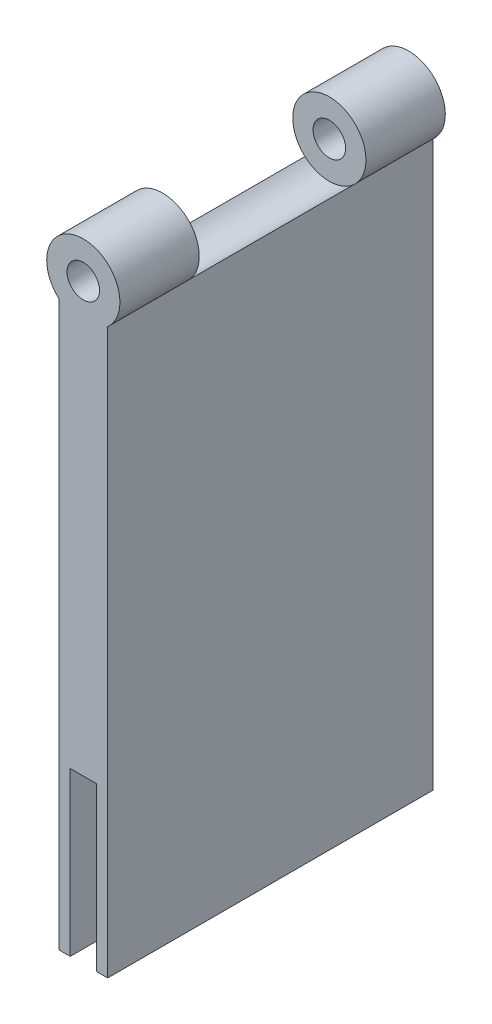
SolidWorks part; units mm, degrees
ref_plane "Front Plane" through (0, 0, 0) normal (0, 0, 1) x (1, 0, 0)
ref_plane "Top Plane" through (0, 0, 0) normal (0, 1, 0) x (1, 0, 0)
ref_plane "Right Plane" through (0, 0, 0) normal (1, 0, 0) x (0, 0, -1)
sketch "Sketch1" plane through (0, 0, 0) normal (0, 1, 0) x (1, 0, 0)
  line L1 (-42.1912, 29.4821) -> (-36.1912, 29.4821)
  line L2 (-42.1912, 29.4821) -> (-42.1912, -10.5179)
  line L3 (-42.1912, -10.5179) -> (-36.1912, -10.5179)
  line L4 (-36.1912, 29.4821) -> (-36.1912, -10.5179)
  line L5 (-42.1912, 29.4821) -> (-36.1912, -10.5179) construction
  line L6 (-42.1912, -10.5179) -> (-36.1912, 29.4821) construction
  point P0 (-39.1912, 9.4821)
  dimension "D1" = 40
  dimension "D2" = 6
extrude "Boss-Extrude1" add sketch "Sketch1" along normal blind 60
sketch "Sketch2" plane through (0, 0, 0) normal (0, -1, 0) x (1, 0, 0)
  line L0 (-39.1912, 10.5179) -> (-37.5956, 10.5179) construction
  line L1 (-42.1912, 10.5179) -> (-36.1912, 10.5179) construction
  line L2 (-40.7956, -29.4821) -> (-40.7956, 10.5179)
  line L3 (-40.7956, -29.4821) -> (-37.5956, -29.4821)
  line L4 (-40.7956, 10.5179) -> (-37.5956, 10.5179)
  line L5 (-37.5956, -29.4821) -> (-37.5956, 10.5179)
  line L6 (-40.7956, -29.4821) -> (-37.5956, 10.5179) construction
  line L7 (-40.7956, 10.5179) -> (-37.5956, -29.4821) construction
  point P5 (-39.1956, -9.4821)
  dimension "D1" = 40
  dimension "D2" = 3.2
extrude "Cut-Extrude2" cut sketch "Sketch2" against normal blind 20
sketch "Sketch3" plane through (0, 0, 10.5179) normal (0, 0, 1) x (1, 0, 0)
  circle A0 centre (-39.1912, 57.6878) radius 2
extrude "Cut-Extrude3" cut sketch "Sketch3" against normal through all both and the other way through all
sketch "Sketch4" plane through (0, 0, 10.5179) normal (0, 0, 1) x (1, 0, 0)
  circle A0 centre (-39.1912, 57.6878) radius 4.5
  dimension "D1" = 9
extrude "Boss-Extrude2" add sketch "Sketch4" against normal blind 40
sketch "Sketch6" plane through (0, 0, 10.5179) normal (0, 0, 1) x (1, 0, 0)
  circle A0 centre (-39.1912, 57.6878) radius 2
extrude "Cut-Extrude4" cut sketch "Sketch6" against normal blind 40
sketch "Sketch7" plane through (-36.1912, 0, 0) normal (1, 0, 0) x (0, 0, -1)
  line L0 (-0.5196, 55.0421) -> (19.4837, 54.3337)
  line L1 (29.4821, 54.3337) -> (-10.5179, 54.3337) construction
  line L2 (-0.7635, 55.0378) -> (-0.7635, 61.6878)
  line L3 (-0.7635, 55.0378) -> (19.7277, 55.0378)
  line L4 (-0.7635, 61.6878) -> (19.7277, 61.6878)
  line L5 (19.7277, 55.0378) -> (19.7277, 61.6878)
  line L6 (-0.7635, 55.0378) -> (19.7277, 61.6878) construction
  line L7 (-0.7635, 61.6878) -> (19.7277, 55.0378) construction
  line L8 (-10.5179, 54.3337) -> (-10.866, 61.6878)
  point P5 (9.4821, 54.6879)
  point P6 (9.4821, 58.3628)
  dimension "D1" = 6.65
extrude "Cut-Extrude5" cut sketch "Sketch7" against normal through all both and the other way through all contours L2 L3 L5 L4
sketch "Sketch8" plane through (0, 0, 0.7635) normal (0, 0, -1) x (-1, 0, 0)
  circle A0 centre (39.1912, 57.6878) radius 4.5
extrude "Cut-Extrude6" cut sketch "Sketch8" along normal up to surface (20.4912 mm away) up to face at (-39.1912, 58.544, -19.7277)
sketch "Sketch9" plane through (0, 0, 0) normal (0, -1, 0) x (1, 0, 0)
  line L1 (-42.1912, 10.5179) -> (-40.7956, 10.5179)
  line L2 (-42.1912, 10.5179) -> (-42.1912, -29.4821)
  line L3 (-42.1912, -29.4821) -> (-40.7956, -29.4821)
  line L4 (-40.7956, 10.5179) -> (-40.7956, -29.4821)
  line L5 (-37.5956, 10.5179) -> (-36.1912, 10.5179)
  line L6 (-37.5956, 10.5179) -> (-37.5956, -29.4821)
  line L7 (-37.5956, -29.4821) -> (-36.1912, -29.4821)
  line L8 (-36.1912, 10.5179) -> (-36.1912, -29.4821)
extrude "Boss-Extrude3" add sketch "Sketch9" along normal blind 15
sketch "Sketch10" plane through (0, 20, 0) normal (0, -1, 0) x (1, 0, 0)
  line L1 (-40.7956, 10.5179) -> (-37.5956, 10.5179)
  line L2 (-40.7956, 10.5179) -> (-40.7956, -29.4821)
  line L3 (-40.7956, -29.4821) -> (-37.5956, -29.4821)
  line L4 (-37.5956, 10.5179) -> (-37.5956, -29.4821)
extrude "Boss-Extrude4" add sketch "Sketch10" along normal blind 15
